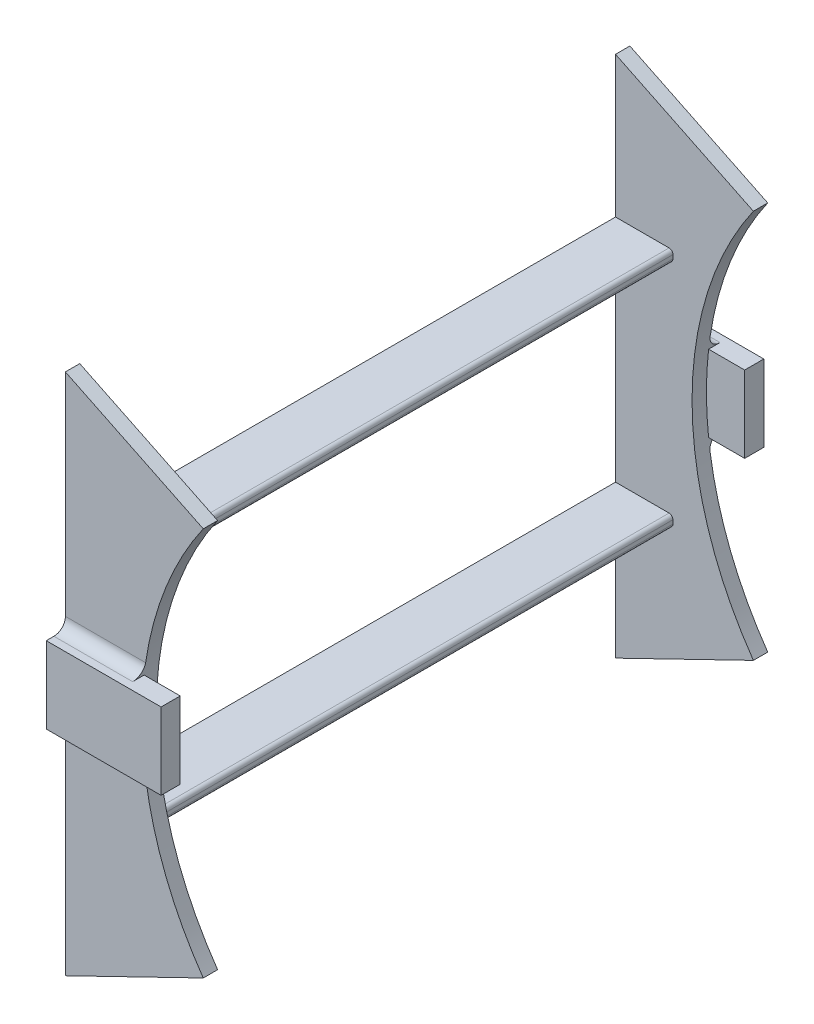
SolidWorks part; units mm, degrees
material "ABS"
ref_plane "Front Plane" through (0, 0, 0) normal (0, 0, 1) x (1, 0, 0)
ref_plane "Top Plane" through (0, 0, 0) normal (0, 1, 0) x (1, 0, 0)
ref_plane "Right Plane" through (0, 0, 0) normal (1, 0, 0) x (0, 0, -1)
sketch "Sketch1" plane through (0, 0, 0) normal (0, 0, 1) x (1, 0, 0)
  line L0 (0, 0) -> (-88.611, 0) construction
  line L1 (-88.611, 0) -> (-108.611, 0) construction
  line L2 (-72.5859, -50.8252) -> (-108.611, -50.8252) construction
  line L3 (-108.611, -50.8252) -> (-108.611, -68.3252) construction
  line L4 (-72.5859, -50.8252) -> (-108.611, -68.3252)
  line L5 (-108.611, -68.3252) -> (-108.611, 68.3252)
  line L6 (-108.611, 50.8252) -> (-108.611, 68.3252) construction
  line L7 (-72.5859, 50.8252) -> (-108.611, 50.8252) construction
  line L8 (-72.5859, 50.8252) -> (-108.611, 68.3252)
  line L9 (0, 0) -> (-83.2671, 30.3067) construction
  line L10 (0, 0) -> (-83.2671, -30.3067) construction
  circle A0 centre (0, 0) radius 88.611 construction
  arc A1 (-72.5859, 50.8252) -> (-72.5859, -50.8252) centre (0, 0) ccw
  point P14 (-88.611, 0)
  dimension "D1" = 177.222
  dimension "D2" = 20
  dimension "D3" = 17.5
  dimension "D4" = 20
extrude "Boss-Extrude1" add sketch "Sketch1" along normal mid plane 3.75
ref_plane "Plane1" through (-83.2671, 0, 0) normal (1, 0, 0) x (0, 0, -1)
sketch "Sketch2" plane through (-83.2671, 0, 0) normal (1, 0, 0) x (0, 0, -1)
  circle A0 centre (0, 30.3067) radius 0.75
  dimension "D1" = 1.5
sketch "Sketch3" plane through (0, 0, 1.875) normal (0, 0, 1) x (1, 0, 0)
  line L0 (0, 0) -> (-108.611, 0) construction
  line L1 (-108.611, 68.3252) -> (-108.611, -68.3252) construction
  line L2 (-108.611, 0) -> (-93.611, 0) construction
  line L3 (-93.611, 0) -> (-93.611, -30) construction
  line L4 (-93.611, -30) -> (-108.611, -30) construction
  line L5 (-108.611, -68.3252) -> (-108.611, 68.3252) construction
  line L6 (-108.611, -31.5) -> (-94.611, -31.5)
  line L7 (-108.611, -31.5) -> (-108.611, -28.5)
  line L8 (-108.611, -28.5) -> (-94.611, -28.5)
  line L9 (-93.611, -30.5) -> (-93.611, -29.5)
  line L10 (-108.611, -31.5) -> (-93.611, -28.5) construction
  line L11 (-108.611, -28.5) -> (-93.611, -31.5) construction
  arc A0 (-94.611, -28.5) -> (-93.611, -29.5) centre (-94.611, -29.5) cw
  arc A1 (-94.611, -31.5) -> (-93.611, -30.5) centre (-94.611, -30.5) ccw
  point P5 (-101.111, -30)
  dimension "D3" = 3
  dimension "D4" = 1
  dimension "D1" = 15
  dimension "D2" = 30
extrude "Boss-Extrude3" add sketch "Sketch3" along normal blind 140
mirror "Mirror2" about plane through (0, 0, 0) normal (0, 1, 0) of "Boss-Extrude3"
sketch "Sketch6" plane through (-83.2671, 0, 0) normal (1, 0, 0) x (0, 0, -1)
  line L0 (0, 0) -> (-1.875, 0)
  line L1 (-1.875, 0) -> (-71.875, 0)
  line L2 (-71.875, 0) -> (-71.875, -50000) construction
  dimension "D1" = 1.875
  dimension "D2" = 70
ref_plane "Plane2" through (0, 0, 71.875) normal (0, 0, 1) x (0, -1, 0)
mirror "Mirror7" about plane through (0, 0, 71.875) normal (0, 0, 1) of "Boss-Extrude1"
sketch "Sketch4" plane through (0, 0, -1.875) normal (0, 0, -1) x (-1, 0, 0)
  line L0 (0, 0) -> (108.611, 0) construction
  line L1 (108.611, 68.3252) -> (108.611, -68.3252) construction
  line L2 (108.611, 0) -> (108.611, 10)
  line L3 (108.611, 0) -> (108.611, -10)
  line L4 (108.611, -10) -> (78.611, -10)
  line L5 (78.611, -10) -> (78.611, 10)
  line L6 (78.611, 10) -> (108.611, 10)
  dimension "D1" = 10
  dimension "D2" = 10
  dimension "D3" = 30
extrude "Boss-Extrude4" add sketch "Sketch4" along normal blind 5
mirror "Mirror10" about plane through (0, 0, 71.875) normal (0, 0, 1) of "Boss-Extrude4"
fillet "Fillet4" radius 3 4 edges at (-98.328, -10, -1.875) (-98.328, 10, -1.875) (-98.328, 10, 145.625) (-98.328, -10, 145.625)
equation "\"OuterThickness\"= 3mm"
equation "\"MasterFillet\"= 3mm"
equation "\"PartSeperation\"= 6mm"
equation "\"Tolerance\"= 0.15mm"
equation "\"HeightPart\"= 100mm"
equation "\"Holes\"= 1.5mm"
equation "\"SpineHolderThickness\"= 3mm"
equation "\"SpineHolderDepth\" = 3mm"
equation "\"MotorLength\" = 40.5mm"
equation "\"MotorWidth\" = 20.3mm"
equation "\"AttachmentHeight\"= 3mm"
equation "\"SpoolDiameter\"= 60mm"
equation "\"SpoolHeight\"= 2mm"
equation "\"SpoolRidgeHeight\"= 1mm"
equation "\"SpoolRidgeDepth\"= 2mm"
equation "\"SpoolSeperation\"= 2mm"
equation "\"ServoHolderWidthOffset\"= 20mm"
equation "\"MotorTransmitterToScrew\"= 21.7mm"
equation "\"SpoolToSpine\"= 15mm"
equation "\"SpoolCenterToMotor\" = 31.5mm"
equation "\"HubOffset\"= 18mm"
equation "\"D1@Sketch1\"=2*(((\"SpoolToSpine\"+\"SpoolDiameter\"/2+\"SpoolRidgeDepth\" -\"SpoolCenterToMotor\" -((\"MotorLength\"+\"ServoHolderWidthOffset\")-(\"MotorLength\"+\"Tolerance\"*2))/2 +(\"MotorLength\"+\"ServoHolderWidthOffset\"))^2 + (\"MotorTransmitterToScrew\"+3)^2)^(1/2)+\"HubOffset\")"
equation "\"D1@Boss-Extrude1\"=\"SpineHolderDepth\"*1.25"
equation "\"D1@Sketch2\"=\"SpineHolderDepth\"*0.5"
equation "\"D1@Boss-Extrude3\"=(3*((\"SpoolDiameter\"/3)*2+\"SpoolRidgeDepth\"*2+\"SpoolSeperation\")+\"SpoolSeperation\")"
equation "\"D1@Sketch6\"=(\"SpineHolderThickness\"*1.25)/2"
equation "\"D2@Sketch6\"=((3*((\"SpoolDiameter\"/3)*2+\"SpoolRidgeDepth\"*2+\"SpoolSeperation\")+\"SpoolSeperation\"))/2"
equation "\"DiscThickness\"= 4mm"
equation "\"LigamentThickness\"= 2mm"
equation "\"LigamentExtension\"= 1mm"
equation "\"LigamentAngle\"= 20deg"
equation "\"SpineDiameter\"= 15mm"
equation "\"LigamentDepth\"= 1mm"
equation "\"ServoFastenerHolders\"=2mm"
equation "\"ArduinoLength\" = 53.4mm"
equation "\"ArduinoWidth\" = 50mm"
equation "\"ArdYOffset\" = 29.5mm"
equation "\"ArdXOffset\" = 20.5mm"
equation "\"ArdXOffsetSmall\" = 25mm"
equation "\"MiddleServoOffset\"= 12mm"
equation "\"LargeServoOffset\"= 3mm"
equation "\"SmallServoOffset\"= 0mm"
equation "\"ToolHoleDiameter\"= 12mm"
equation "\"D1\" = \"SpineHolderDepth\" / 4"
equation "\"OuterDiameter\"= 15mm"
